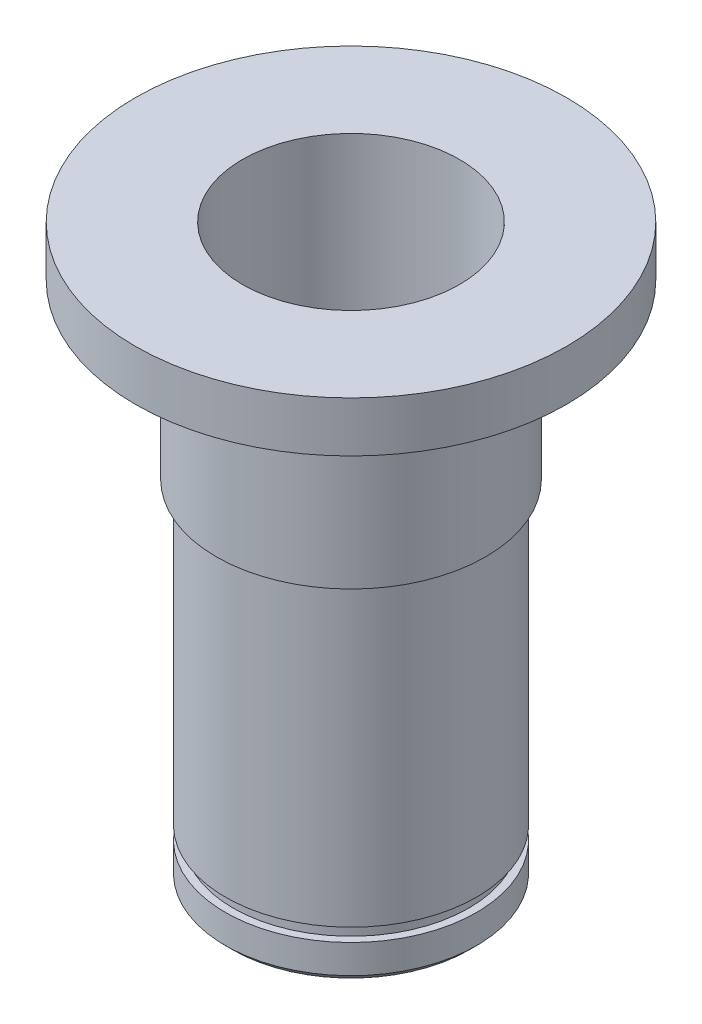
SolidWorks part; units mm, degrees
material "6061-T6 Al"
ref_plane "XY" through (0, 0, 0) normal (0, 0, 1) x (1, 0, 0)
ref_plane "XZ" through (0, 0, 0) normal (0, 1, 0) x (1, 0, 0)
ref_plane "YZ" through (0, 0, 0) normal (1, 0, 0) x (0, 0, -1)
sketch "Sketch1" plane through (0, 0, 0) normal (0, 0, 1) x (1, 0, 0)
  line L0 (0, 18.2828) -> (0, -0.9174) construction
  line L1 (-19.05, 50.4825) -> (-19.05, 46.0375)
  line L2 (-19.05, 46.0375) -> (-11.8999, 46.0375)
  line L3 (-11.0998, 30.7975) -> (-11.0998, 0)
  line L4 (-11.0998, 0) -> (-9.5885, 0)
  line L5 (-9.5885, 0) -> (-9.5885, 50.4825)
  line L6 (-9.5885, 50.4825) -> (-19.05, 50.4825)
  line L7 (-11.8999, 46.0375) -> (-11.8999, 30.7975)
  line L8 (-11.8999, 30.7975) -> (-11.0998, 30.7975)
  dimension "D1" = 19.177
  dimension "D2" = 22.1996
  dimension "D3" = 38.1
  dimension "D4" = 15.24
  dimension "D5" = 4.445
  dimension "D6" = 46.0375
  dimension "D7" = 23.7998
revolve "Revolve1" add sketch "Sketch1" angle 360 about L0
chamfer "Chamfer1" distance 0.635 angle 45 1 edges at (0, 0, 11.0998)
sketch "Sketch3" plane through (0, 0, 0) normal (0, 0, 1) x (1, 0, 0)
  line L0 (0, -2.0701) -> (0, 15.9218) construction
  line L1 (-10.4648, 0) -> (10.4648, 0) construction
  line L2 (-11.0998, 3.175) -> (-10.4267, 3.175)
  line L3 (-11.0998, 3.175) -> (-11.0998, 4.3434)
  line L4 (-11.0998, 4.3434) -> (-10.4267, 4.3434)
  line L5 (-10.4267, 3.175) -> (-10.4267, 4.3434)
  line L6 (-11.0998, 30.7975) -> (-11.0998, 0.635) construction
  dimension "D1" = 20.8534
  dimension "D2" = 1.1684
  dimension "D3" = 3.175
revolve "Cut-Revolve1" cut sketch "Sketch3" angle 360 about L0
fillet "Fillet1" radius 0.3969 2 edges at (0, 46.0375, 11.8999) (0, 30.7975, 11.0998)
